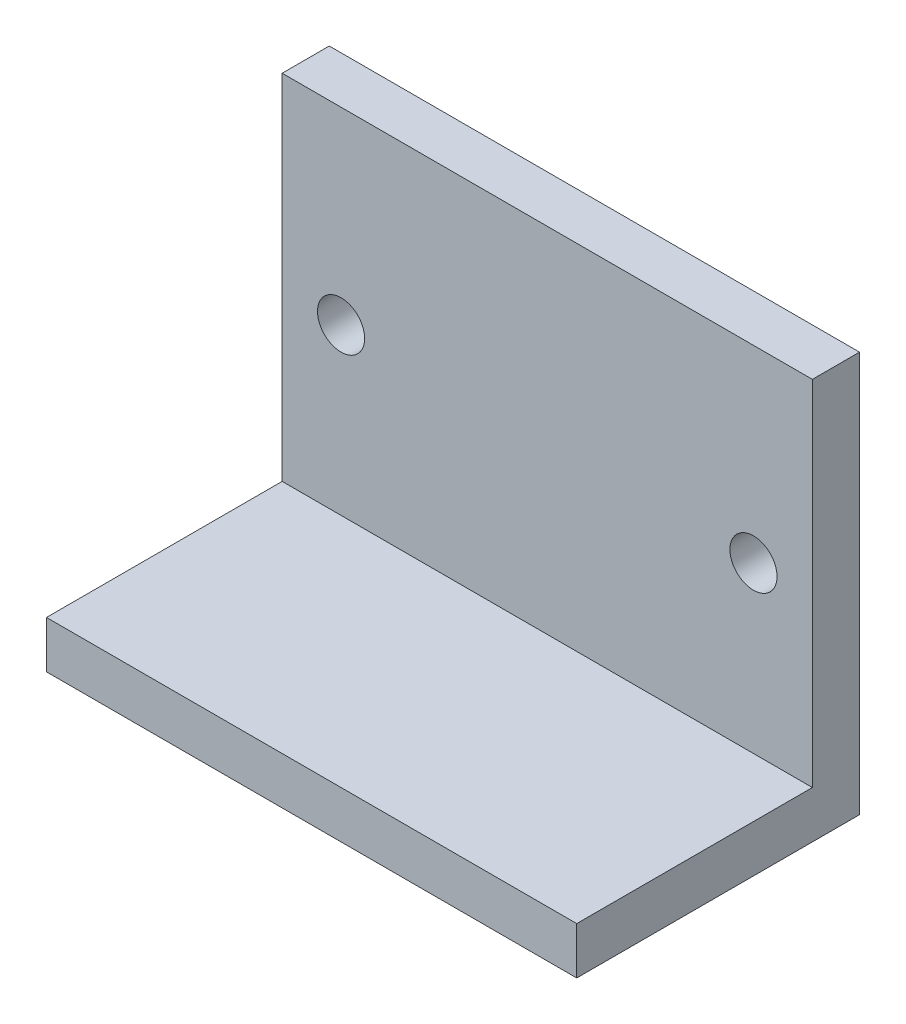
SolidWorks part; units mm, degrees
ref_plane "Front Plane" through (0, 0, 0) normal (0, 0, 1) x (1, 0, 0)
ref_plane "Top Plane" through (0, 0, 0) normal (0, 1, 0) x (1, 0, 0)
ref_plane "Right Plane" through (0, 0, 0) normal (1, 0, 0) x (0, 0, -1)
sketch "Sketch1" plane through (0, 0, 0) normal (0, 0, 1) x (1, 0, 0)
  line L1 (0, 34) -> (45, 34)
  line L2 (0, 34) -> (0, 0)
  line L3 (0, 0) -> (45, 0)
  line L4 (45, 34) -> (45, 0)
  dimension "D1" = 45
  dimension "D2" = 34
extrude "Boss-Extrude1" add sketch "Sketch1" along normal blind 4
sketch "Sketch2" plane through (0, 0, 4) normal (0, 0, 1) x (1, 0, 0)
  line L0 (45, 0) -> (45, 34) construction
  line L1 (0, 0) -> (45, 0)
  line L2 (0, 0) -> (0, 4)
  line L3 (0, 4) -> (45, 4)
  line L4 (45, 0) -> (45, 4)
  dimension "D1" = 4
extrude "Boss-Extrude2" add sketch "Sketch2" along normal blind 20
sketch "Sketch3" plane through (0, 0, 4) normal (0, 0, 1) x (1, 0, 0)
  line L0 (0, 34) -> (0, 4) construction
  line L1 (45, 4) -> (45, 34) construction
  line L2 (45, 4) -> (0, 4) construction
  circle A0 centre (5, 18) radius 2
  circle A1 centre (40, 18) radius 2
  point P8 (5, 23.081)
  point P9 (0, 0)
  dimension "D1" = 4
  dimension "D2" = 4
  dimension "D3" = 5
  dimension "D4" = 5
  dimension "D5" = 14
extrude "Cut-Extrude1" cut sketch "Sketch3" against normal blind 10
